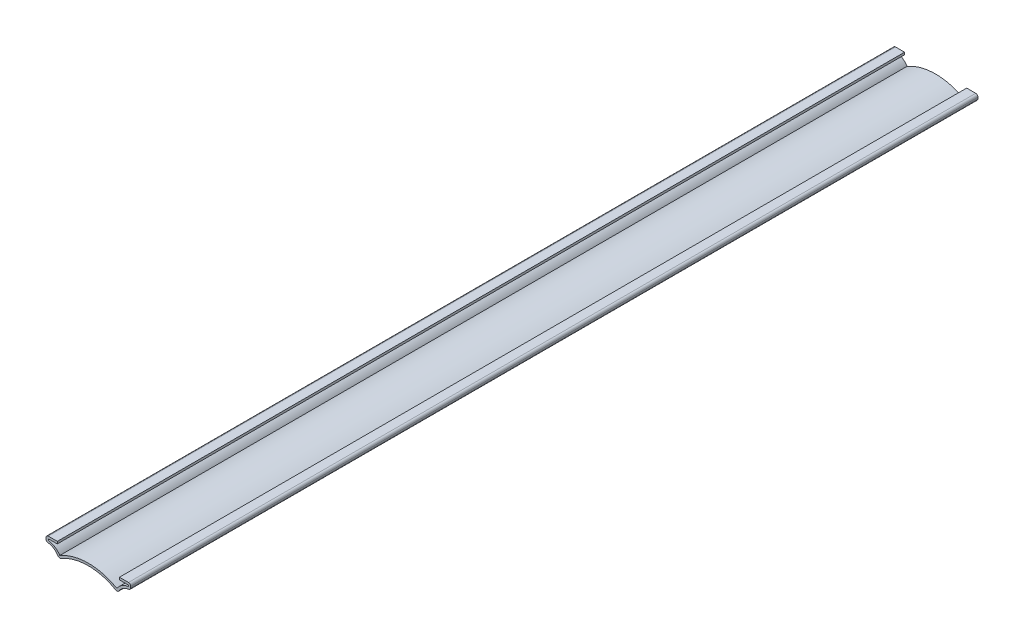
SolidWorks part; units mm, degrees
ref_plane "Front Plane" through (0, 0, 0) normal (0, 0, 1) x (1, 0, 0)
ref_plane "Top Plane" through (0, 0, 0) normal (0, 1, 0) x (1, 0, 0)
ref_plane "Right Plane" through (0, 0, 0) normal (1, 0, 0) x (0, 0, -1)
sketch "Sketch1" plane through (0, 0, 0) normal (0, 0, 1) x (1, 0, 0)
  line L0 (0, 0) -> (0, 15.5104) construction
  line L1 (0, 0) -> (-17.4625, 0) construction
  line L2 (-17.4625, 0) -> (-23.8125, 0)
  line L3 (-23.8125, 0) -> (-23.8125, -3.175)
  line L4 (0, -3.1498) -> (-5.4213, -3.1498) construction
  arc A0 (-23.8125, -3.175) -> (-16.5377, -7.9375) centre (-23.8125, -11.1125) cw
  arc A1 (-16.5377, -7.9375) -> (0, -3.1498) centre (0, -34.1061) cw
  point P8 (0, -3.1437)
  point P12 (-8.7312, 0)
  point P23 (0, 5.1593)
  dimension "D5" = 7.9375
  dimension "D6" = 30.9562
  dimension "D1" = 47.625
  dimension "D2" = 6.35
  dimension "D3" = 3.175
  dimension "D4" = 4.7625
extrude "Extrude-Thin1" add sketch "Sketch1" against normal blind 476.25 thin contours L2 L3 A0 A1 thin type one direction reverse wall 1.27
mirror "Mirror1" about plane through (0, -1.8798, -476.25) normal (-1, 0, 0) of bodies 102
fillet "Fillet1" radius 1.27 6 edges at (23.8125, -3.175, -238.125) (23.8125, 0, -238.125) (16.5377, -7.9375, -238.125) (-16.5377, -7.9375, -238.125) (-23.8125, -3.175, -238.125) (-23.8125, 0, -238.125)
